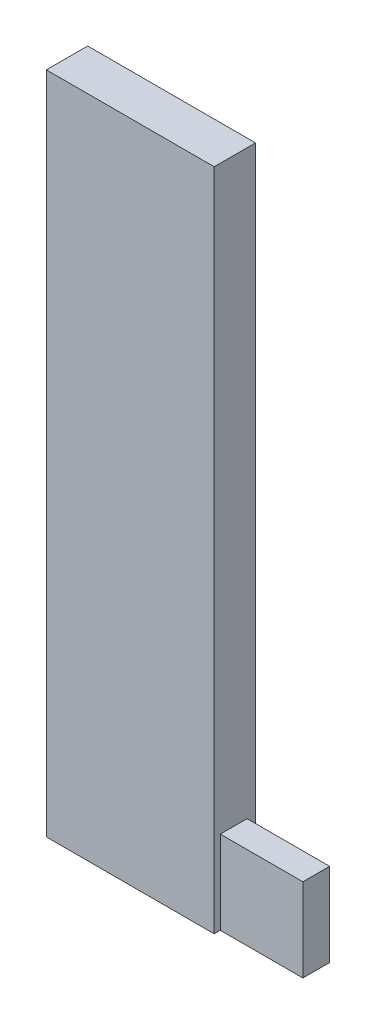
SolidWorks part; units mm, degrees
ref_plane "Front Plane" through (0, 0, 0) normal (0, 0, 1) x (1, 0, 0)
ref_plane "Top Plane" through (0, 0, 0) normal (0, 1, 0) x (1, 0, 0)
ref_plane "Right Plane" through (0, 0, 0) normal (1, 0, 0) x (0, 0, -1)
sketch "Sketch1" plane through (0, 0, 0) normal (0, 0, 1) x (1, 0, 0)
  line L0 (-37.5648, 18.053) -> (-32.4024, 18.053)
  line L3 (-37.5648, -2.382) -> (-37.5648, 18.053)
  line L6 (-37.5648, 18.053) -> (-32.4024, 18.053)
  line L7 (-37.5648, 18.053) -> (-37.5648, -2.382)
  line L8 (-37.5648, -2.382) -> (-32.4024, -2.382)
  line L9 (-32.4024, 18.053) -> (-32.4024, -2.382)
  line L12 (-32.4024, 16.6244) -> (-32.4024, -2.382)
  line L15 (-32.4024, -2.382) -> (-37.5648, -2.382)
extrude "Boss-Extrude1" add sketch "Sketch1" along normal blind 1.27 contours L7 L6 L9 L8
sketch "Sketch2" plane through (-37.5648, 0, 0) normal (-1, 0, 0) x (0, 0, 1)
  line L10 (0.1917, 16.874) -> (1.0307, 16.874)
  line L11 (0.1917, 16.874) -> (0.1917, 12.9918)
  line L12 (0.1917, 12.9918) -> (1.0307, 12.9918)
  line L13 (1.0307, 16.874) -> (1.0307, 12.9918)
extrude "Cut-Extrude1" cut sketch "Sketch2" against normal blind 3.81
sketch "Sketch3" plane through (-32.4024, 0, 0) normal (1, 0, 0) x (0, 0, -1)
  line L0 (-1.0823, -2.382) -> (-1.0823, 0.1815)
  line L1 (-1.27, -2.382) -> (0, -2.382) construction
  line L2 (-1.0823, 0.1815) -> (-0.2593, 0.1815)
  line L3 (-0.2593, 0.1815) -> (-0.2593, -2.382)
  line L4 (-0.2593, -2.382) -> (-1.0823, -2.382)
extrude "Boss-Extrude2" add sketch "Sketch3" along normal blind 2.54
